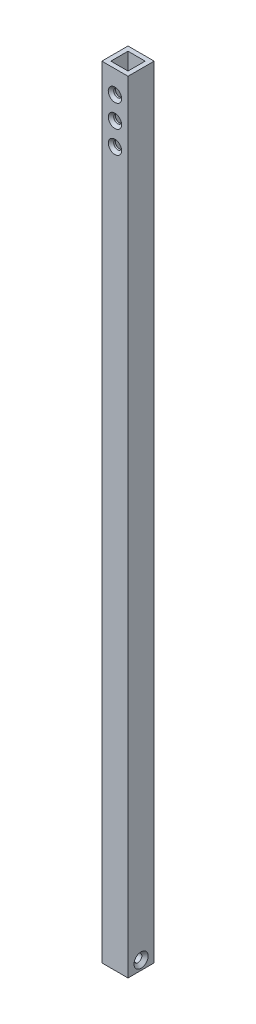
SolidWorks part; units mm, degrees
material "1060 Alloy"
ref_plane "Front Plane" through (0, 0, 0) normal (0, 0, 1) x (1, 0, 0)
ref_plane "Top Plane" through (0, 0, 0) normal (0, 1, 0) x (1, 0, 0)
ref_plane "Right Plane" through (0, 0, 0) normal (1, 0, 0) x (0, 0, -1)
sketch "Sketch1" plane through (0, 0, 0) normal (0, 1, 0) x (1, 0, 0)
  line L0 (0, 0) -> (0, 9.23) construction
  line L1 (-9.23, -9.23) -> (9.23, -9.23)
  line L2 (-9.23, -9.23) -> (-9.23, 9.23)
  line L3 (-9.23, 9.23) -> (9.23, 9.23)
  line L4 (9.23, -9.23) -> (9.23, 9.23)
  line L5 (0, 0) -> (9.23, 0) construction
  line L7 (-6.055, -6.055) -> (6.055, -6.055)
  line L8 (-6.055, -6.055) -> (-6.055, 6.055)
  line L9 (-6.055, 6.055) -> (6.055, 6.055)
  line L10 (6.055, -6.055) -> (6.055, 6.055)
  dimension "D1" = 18.46
  dimension "D2" = 3.175
extrude "Boss-Extrude1" add sketch "Sketch1" along normal blind 550.5
sketch "Sketch2" plane through (0, 0, 0) normal (0, -1, 0) x (1, 0, 0)
  line L1 (6.055, 6.055) -> (-6.055, 6.055)
  line L2 (6.055, 6.055) -> (6.055, -6.055)
  line L3 (6.055, -6.055) -> (-6.055, -6.055)
  line L4 (-6.055, 6.055) -> (-6.055, -6.055)
extrude "Boss-Extrude2" add sketch "Sketch2" against normal blind 12.7
sketch "Sketch4" plane through (0, 0, 0) normal (0, 0, 1) x (1, 0, 0)
  line L0 (-9.23, 6.365) -> (32.4713, 6.365) construction
  line L1 (-9.23, 6.365) -> (9.23, 6.365)
  line L2 (-9.23, 6.365) -> (-9.23, 3.59)
  line L3 (-9.23, 3.59) -> (7.005, 3.59)
  line L4 (7.005, 3.59) -> (9.23, 1.365)
  line L5 (9.23, 1.365) -> (9.23, 6.365)
  line L6 (9.23, 550.5) -> (9.23, 0) construction
  line L7 (-9.23, 550.5) -> (-9.23, 0) construction
  dimension "D1" = 5.55
  dimension "D2" = 3.59
  dimension "D3" = 10
  dimension "D4" = 45
revolve "Cut-Revolve1" cut sketch "Sketch4" angle 360 about L0
sketch "Sketch5" plane through (0, 0, 0) normal (1, 0, 0) x (0, 0, -1)
  line L0 (-7.305, 537.35) -> (-9.23, 539.275)
  line L1 (9.23, 534.575) -> (-9.23, 534.575)
  line L2 (9.23, 534.575) -> (9.23, 537.35)
  line L3 (9.23, 537.35) -> (-7.305, 537.35)
  line L4 (-9.23, 534.575) -> (-26.1459, 534.575) construction
  line L5 (-9.23, 539.275) -> (-9.23, 534.575)
  line L6 (-9.23, 550.5) -> (-9.23, 0) construction
  line L7 (9.23, 550.5) -> (9.23, 0) construction
  line L8 (-9.23, 550.5) -> (9.23, 550.5) construction
  dimension "D1" = 45
  dimension "D2" = 9.4
  dimension "D3" = 5.55
  dimension "D4" = 13.15
revolve "Cut-Revolve2" cut sketch "Sketch5" angle 360 about L4
pattern_linear "LPattern1" count 3 spacing 15.9 along (0, -1, 0) of "Cut-Revolve2"
